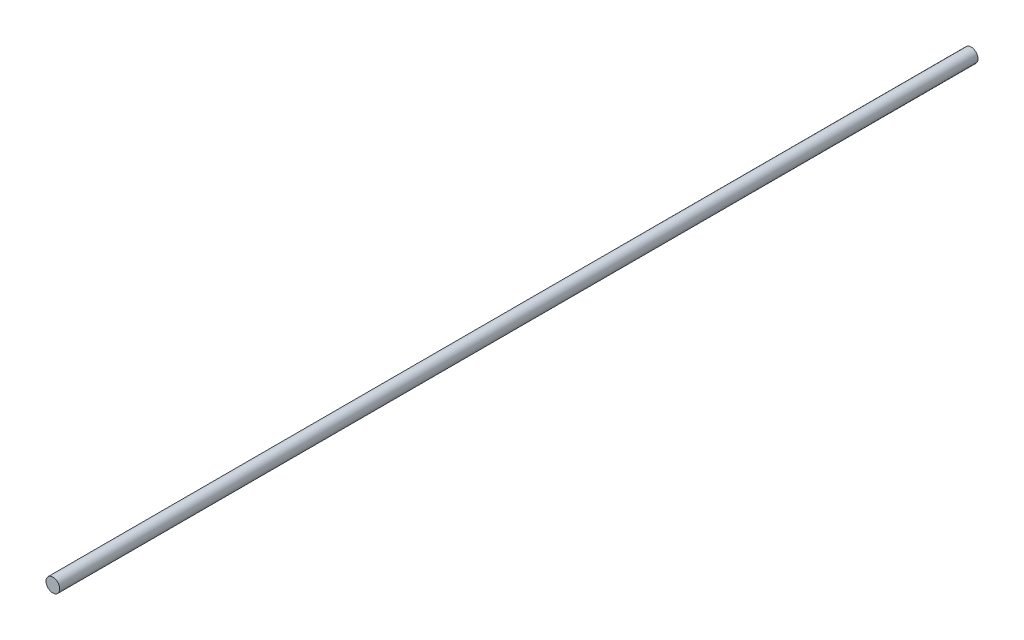
SolidWorks part; units mm, degrees
material "Hexcel AS4C (3000 Filaments)"
ref_plane "Front Plane" through (0, 0, 0) normal (0, 0, 1) x (1, 0, 0)
ref_plane "Top Plane" through (0, 0, 0) normal (0, 1, 0) x (1, 0, 0)
ref_plane "Right Plane" through (0, 0, 0) normal (1, 0, 0) x (0, 0, -1)
sketch "Sketch1" plane through (0, 0, 0) normal (0, 0, 1) x (1, 0, 0)
  circle A0 centre (0, 0) radius 3
  dimension "D1" = 6
extrude "Boss-Extrude1" add sketch "Sketch1" along normal mid plane 400
